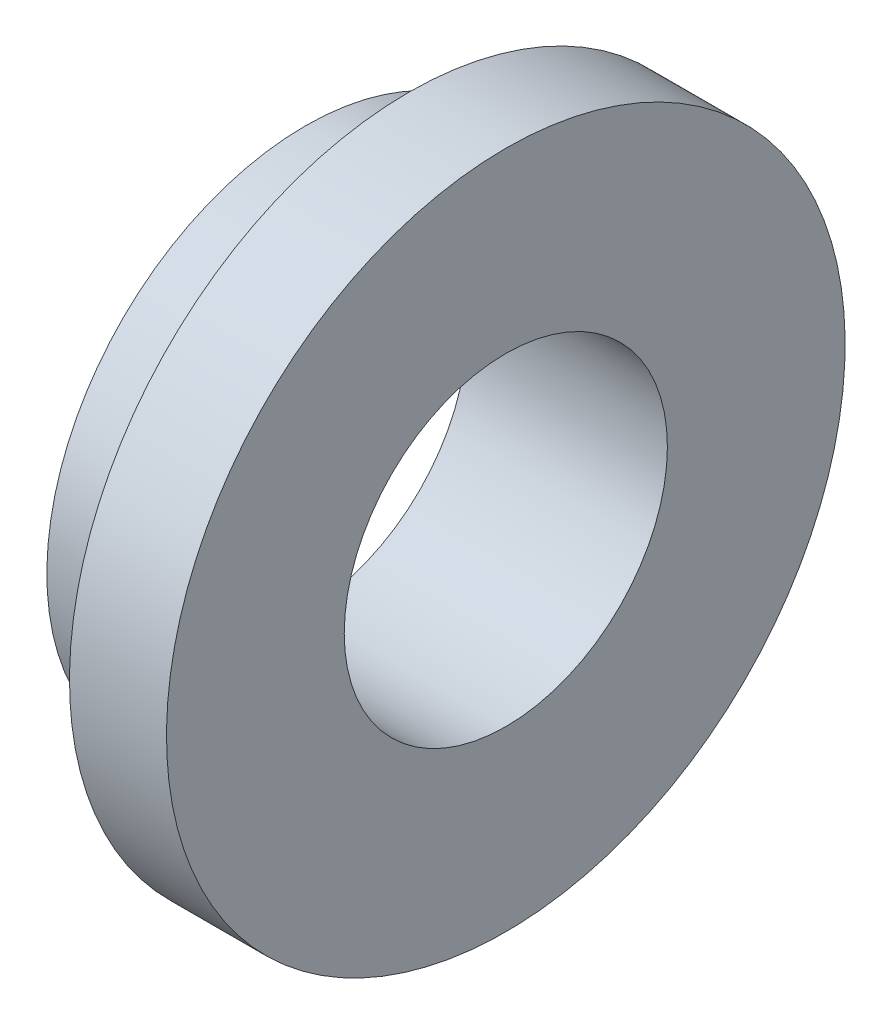
SolidWorks part; units mm, degrees
material "NEOPRENE"
ref_plane "Front Plane" through (0, 0, 0) normal (0, 0, 1) x (1, 0, 0)
ref_plane "Top Plane" through (0, 0, 0) normal (0, 1, 0) x (1, 0, 0)
ref_plane "Right Plane" through (0, 0, 0) normal (1, 0, 0) x (0, 0, -1)
sketch "Sketch1" plane through (0, 0, 0) normal (0, 0, 1) x (1, 0, 0)
  line L0 (-2.4613, 3.175) -> (-1.1913, 3.175)
  line L1 (-1.1913, 3.175) -> (-1.1913, 4.1672)
  line L2 (-1.1913, 4.1672) -> (0, 4.1672)
  line L3 (0, 4.1672) -> (0, 1.9844)
  line L4 (0, 1.9844) -> (-2.4613, 1.9844)
  line L5 (-2.4613, 1.9844) -> (-2.4613, 3.175)
  line L6 (12.9968, 0) -> (-87.8391, 0) construction
  dimension "D1" = 1.9844
  dimension "D2" = 3.175
  dimension "D3" = 1.1913
  dimension "D4" = 1.27
  dimension "D5" = 8.3344
revolve "Revolve1" add sketch "Sketch1" angle 360 about L6
